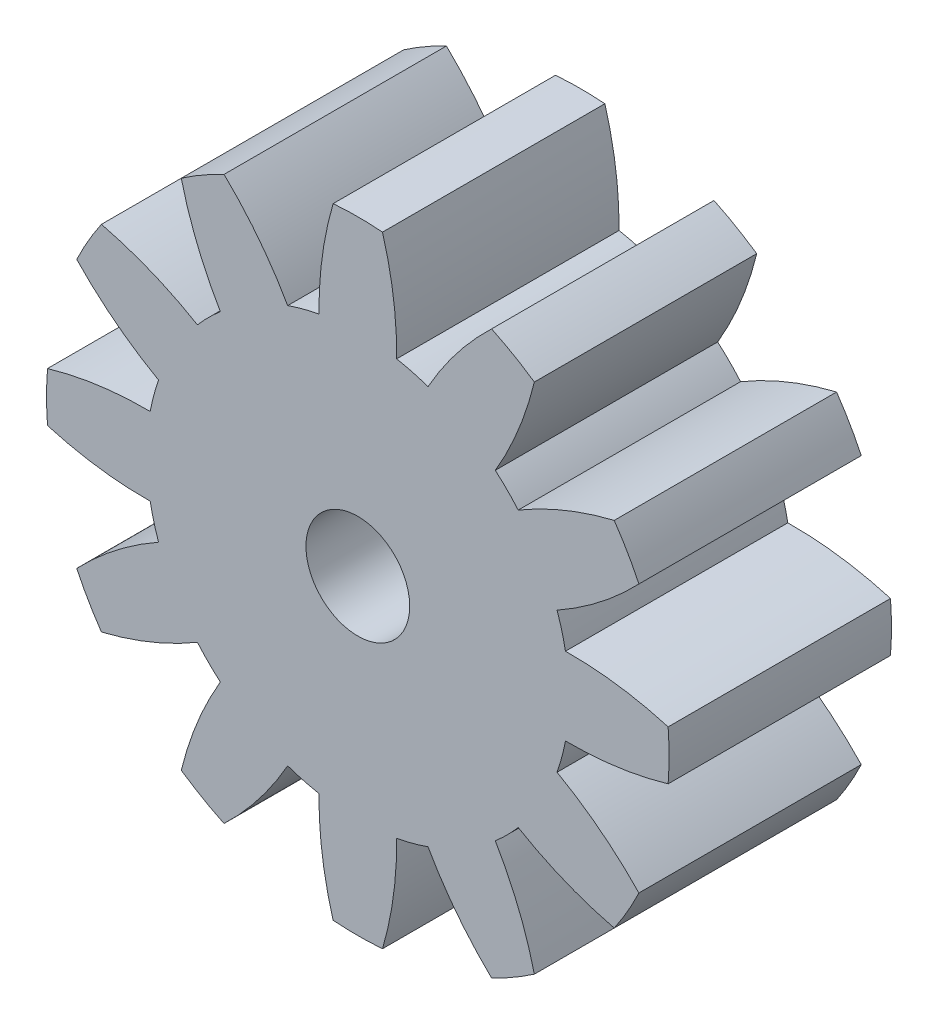
SolidWorks part; units mm, degrees
ref_plane "정면" through (0, 0, 0) normal (0, 0, 1) x (1, 0, 0)
ref_plane "윗면" through (0, 0, 0) normal (0, 1, 0) x (1, 0, 0)
ref_plane "우측면" through (0, 0, 0) normal (1, 0, 0) x (0, 0, -1)
sketch "스케치1" plane through (0, 0, 0) normal (0, 0, 1) x (1, 0, 0)
  line L0 (0, 0) -> (0, 2.1) construction
  line L1 (0, 0) -> (-0.2349, 1.7846) construction
  line L2 (-0.2349, 1.7846) -> (-0.1665, 2.0934) construction
  line L3 (-0.2349, 1.7846) -> (-0.3591, 0.0253) construction
  circle A0 centre (0, 0) radius 1.8 construction
  circle A1 centre (0, 0) radius 2.1 construction
  circle A2 centre (0, 0) radius 1.425 construction
  circle A3 centre (0, 0) radius 0.36 construction
  arc A4 (-0.1665, 2.0934) -> (-0.262, 1.4007) centre (2.1135, 1.426) ccw
  arc A5 (0.1665, 2.0934) -> (0.262, 1.4007) centre (-2.1135, 1.426) cw
  arc A6 (-0.1665, 2.0934) -> (0.1665, 2.0934) centre (0, 0) cw
  circle A40 centre (0, 0) radius 0.35
  arc A41 (1.1909, 1.7297) -> (0.9273, 1.082) centre (-1.1173, 2.2916) cw
  arc A42 (0.9025, 1.8962) -> (1.1909, 1.7297) centre (0, 0) cw
  arc A43 (0.9025, 1.8962) -> (0.4734, 1.3441) centre (2.5433, 0.1782) ccw
  arc A44 (1.8962, 0.9025) -> (1.3441, 0.4734) centre (0.1782, 2.5433) cw
  arc A45 (1.7297, 1.1909) -> (1.8962, 0.9025) centre (0, 0) cw
  arc A46 (1.7297, 1.1909) -> (1.082, 0.9273) centre (2.2916, -1.1173) ccw
  arc A47 (2.0934, -0.1665) -> (1.4007, -0.262) centre (1.426, 2.1135) cw
  arc A48 (2.0934, 0.1665) -> (2.0934, -0.1665) centre (0, 0) cw
  arc A49 (2.0934, 0.1665) -> (1.4007, 0.262) centre (1.426, -2.1135) ccw
  arc A50 (1.7297, -1.1909) -> (1.082, -0.9273) centre (2.2916, 1.1173) cw
  arc A51 (1.8962, -0.9025) -> (1.7297, -1.1909) centre (0, 0) cw
  arc A52 (1.8962, -0.9025) -> (1.3441, -0.4734) centre (0.1782, -2.5433) ccw
  arc A53 (0.9025, -1.8962) -> (0.4734, -1.3441) centre (2.5433, -0.1782) cw
  arc A54 (1.1909, -1.7297) -> (0.9025, -1.8962) centre (0, 0) cw
  arc A55 (1.1909, -1.7297) -> (0.9273, -1.082) centre (-1.1173, -2.2916) ccw
  arc A56 (-0.1665, -2.0934) -> (-0.262, -1.4007) centre (2.1135, -1.426) cw
  arc A57 (0.1665, -2.0934) -> (-0.1665, -2.0934) centre (0, 0) cw
  arc A58 (0.1665, -2.0934) -> (0.262, -1.4007) centre (-2.1135, -1.426) ccw
  arc A59 (-1.1909, -1.7297) -> (-0.9273, -1.082) centre (1.1173, -2.2916) cw
  arc A60 (-0.9025, -1.8962) -> (-1.1909, -1.7297) centre (0, 0) cw
  arc A61 (-0.9025, -1.8962) -> (-0.4734, -1.3441) centre (-2.5433, -0.1782) ccw
  arc A62 (-1.8962, -0.9025) -> (-1.3441, -0.4734) centre (-0.1782, -2.5433) cw
  arc A63 (-1.7297, -1.1909) -> (-1.8962, -0.9025) centre (0, 0) cw
  arc A64 (-1.7297, -1.1909) -> (-1.082, -0.9273) centre (-2.2916, 1.1173) ccw
  arc A66 (-2.0934, 0.1665) -> (-1.4007, 0.262) centre (-1.426, -2.1135) cw
  arc A67 (-2.0934, -0.1665) -> (-2.0934, 0.1665) centre (0, 0) cw
  arc A68 (-2.0934, -0.1665) -> (-1.4007, -0.262) centre (-1.426, 2.1135) ccw
  arc A69 (-1.7297, 1.1909) -> (-1.082, 0.9273) centre (-2.2916, -1.1173) cw
  arc A70 (-1.8962, 0.9025) -> (-1.7297, 1.1909) centre (0, 0) cw
  arc A71 (-1.8962, 0.9025) -> (-1.3441, 0.4734) centre (-0.1782, 2.5433) ccw
  arc A72 (-0.9025, 1.8962) -> (-0.4734, 1.3441) centre (-2.5433, 0.1782) cw
  arc A73 (-1.1909, 1.7297) -> (-0.9025, 1.8962) centre (0, 0) cw
  arc A74 (-1.1909, 1.7297) -> (-0.9273, 1.082) centre (1.1173, 2.2916) ccw
  arc A75 (-0.4734, 1.3441) -> (-0.262, 1.4007) centre (0, 0) cw
  arc A76 (0.262, 1.4007) -> (0.4734, 1.3441) centre (0, 0) cw
  arc A77 (0.9273, 1.082) -> (1.082, 0.9273) centre (0, 0) cw
  arc A78 (1.3441, 0.4734) -> (1.4007, 0.262) centre (0, 0) cw
  arc A79 (1.4007, -0.262) -> (1.3441, -0.4734) centre (0, 0) cw
  arc A80 (1.082, -0.9273) -> (0.9273, -1.082) centre (0, 0) cw
  arc A81 (0.4734, -1.3441) -> (0.262, -1.4007) centre (0, 0) cw
  arc A82 (-0.262, -1.4007) -> (-0.4734, -1.3441) centre (0, 0) cw
  arc A83 (-0.9273, -1.082) -> (-1.082, -0.9273) centre (0, 0) cw
  arc A84 (-1.3441, -0.4734) -> (-1.4007, -0.262) centre (0, 0) cw
  arc A85 (-1.4007, 0.262) -> (-1.3441, 0.4734) centre (0, 0) cw
  arc A86 (-1.082, 0.9273) -> (-0.9273, 1.082) centre (0, 0) cw
  point P67 (0, 0)
  point P84 (0, 0)
  point P89 (0, 0)
  point P113 (0, 0)
  dimension "D1" = 3.6
  dimension "D2" = 0.375
  dimension "D3" = 0.3
  dimension "D6" = 0.72
  dimension "D9" = 0.7
  dimension "D4" = 20
  dimension "D5" = 7.5
  dimension "D7" = 12
  dimension "D8" = 12
extrude "보스-돌출1" add sketch "스케치1" along normal blind 1.5
